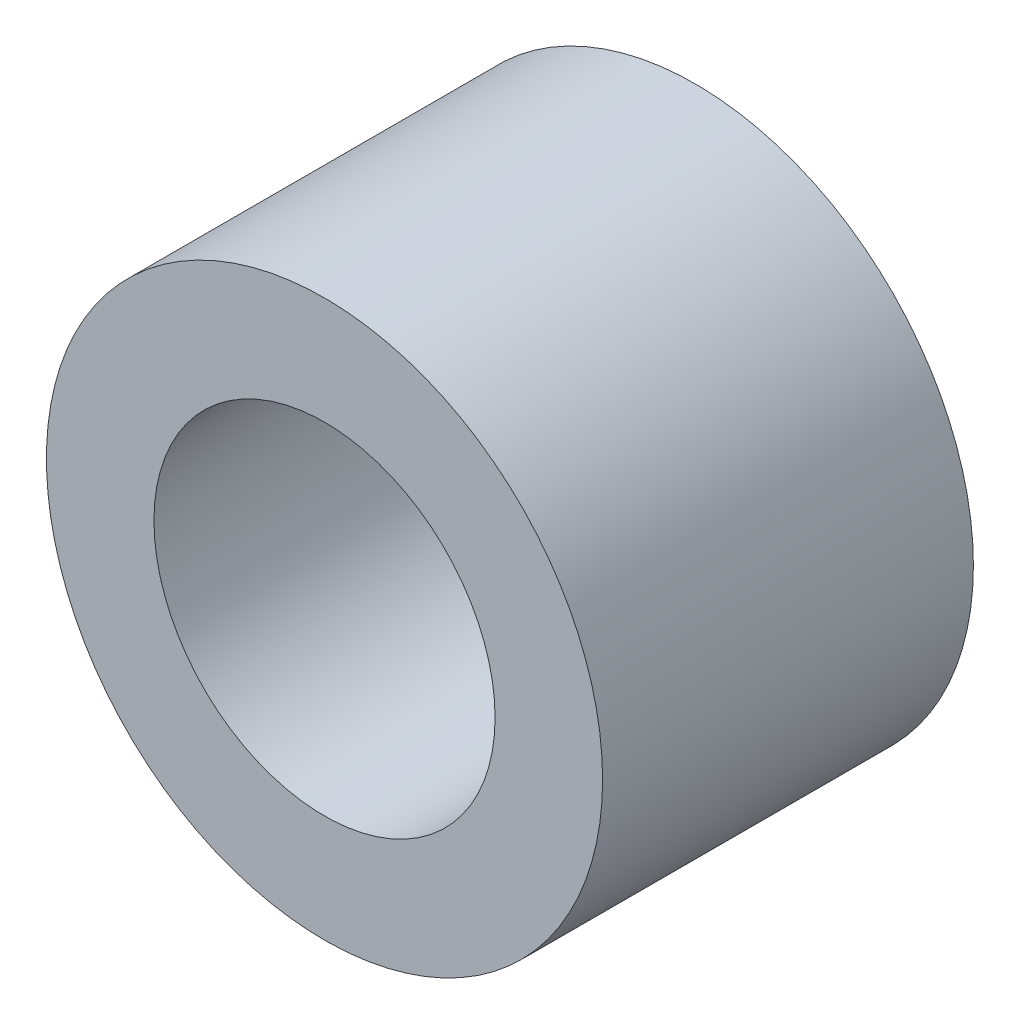
SolidWorks part; units mm, degrees
ref_plane "Front Plane" through (0, 0, 0) normal (0, 0, 1) x (1, 0, 0)
ref_plane "Top Plane" through (0, 0, 0) normal (0, 1, 0) x (1, 0, 0)
ref_plane "Right Plane" through (0, 0, 0) normal (1, 0, 0) x (0, 0, -1)
sketch "Sketch1" plane through (0, 0, 0) normal (0, 0, 1) x (1, 0, 0)
  circle A0 centre (0, 0) radius 2.3813
  circle A1 centre (0, 0) radius 1.4605
  dimension "D1" = 4.7625
  dimension "D2" = 2.921
extrude "Boss-Extrude1" add sketch "Sketch1" along normal blind 3.175
